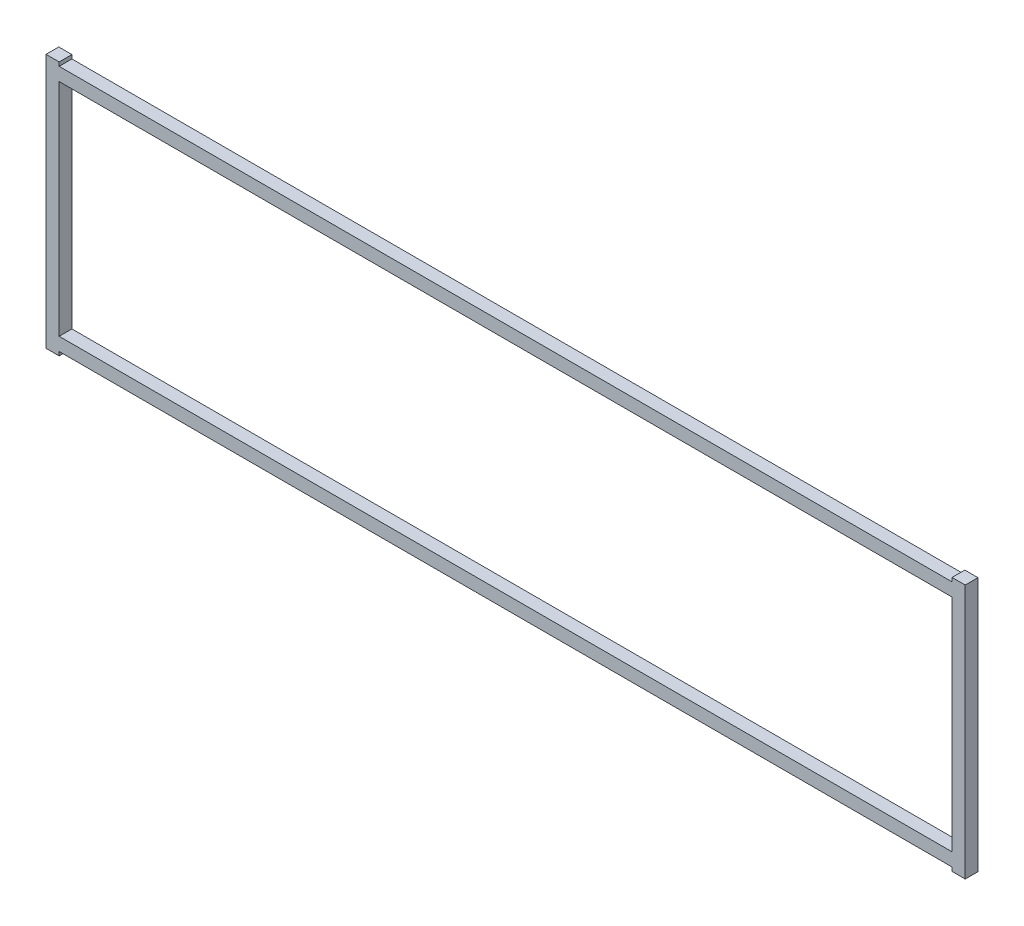
SolidWorks part; units mm, degrees
ref_plane "Front" through (0, 0, 0) normal (0, 0, 1) x (1, 0, 0)
ref_plane "Top" through (0, 0, 0) normal (0, 1, 0) x (1, 0, 0)
ref_plane "Right" through (0, 0, 0) normal (1, 0, 0) x (0, 0, -1)
sketch "Sketch1" plane through (0, 0, 0) normal (0, 0, 1) x (1, 0, 0)
  line L0 (222.1484, -63.354) -> (228.7016, -63.354)
  line L1 (228.7016, -63.354) -> (228.7016, 63.3539)
  line L2 (228.7016, 63.3539) -> (222.1484, 63.3539)
  line L3 (222.1484, 63.3539) -> (222.1484, 61.4458)
  line L4 (222.1484, 61.4458) -> (-222.1484, 61.4458)
  line L5 (-222.1484, 61.4458) -> (-222.1484, 63.3539)
  line L6 (-222.1484, 63.3539) -> (-228.7016, 63.3539)
  line L7 (-228.7016, 63.3539) -> (-228.7016, -63.354)
  line L8 (-228.7016, -63.354) -> (-222.1484, -63.354)
  line L9 (-222.1484, -63.354) -> (-222.1484, -61.4458)
  line L10 (-222.1484, -61.4458) -> (222.1484, -61.4458)
  line L11 (222.1484, -61.4458) -> (222.1484, -63.354)
  line L12 (-222.1484, -54.8926) -> (222.1484, -54.8926)
  line L13 (222.1484, -54.8926) -> (222.1484, 54.8926)
  line L14 (222.1484, 54.8926) -> (-222.1484, 54.8926)
  line L15 (-222.1484, 54.8926) -> (-222.1484, -54.8926)
extrude "Boss-Extrude1" add sketch "Sketch1" along normal blind 6.35
